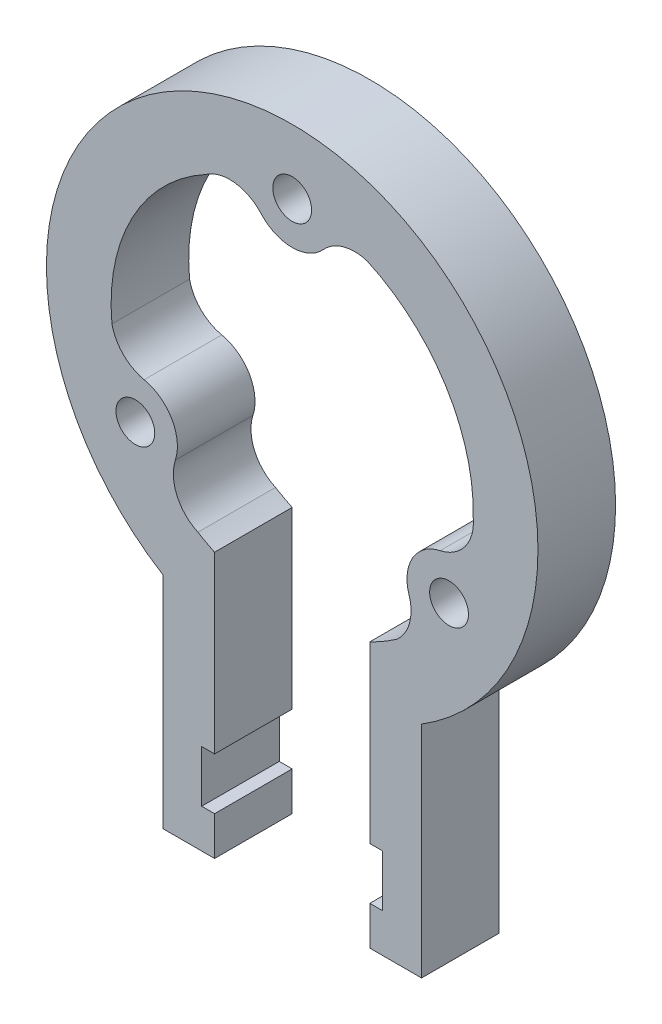
SolidWorks part; units mm, degrees
ref_plane "Plan de face" through (0, 0, 0) normal (0, 0, 1) x (1, 0, 0)
ref_plane "Plan de dessus" through (0, 0, 0) normal (0, 1, 0) x (1, 0, 0)
ref_plane "Plan de droite" through (0, 0, 0) normal (1, 0, 0) x (0, 0, -1)
sketch "Esquisse1" plane through (0, 0, 0) normal (0, 0, 1) x (1, 0, 0)
  line L0 (0, 14) -> (-12.125, -7.0011) construction
  line L1 (-12.125, -7.0011) -> (-10.6244, -7.0011) construction
  line L2 (12.125, -7.0011) -> (0, 14) construction
  line L3 (-6, -33.1555) -> (-6, -30.1555)
  line L5 (10, -16.1555) -> (10, -33.1555)
  line L6 (10, -33.1555) -> (6, -33.1555)
  line L7 (-10, -16.1555) -> (-10, -33.1555)
  line L8 (-7, -26.1555) -> (-6, -26.1555)
  line L9 (-7, -26.1555) -> (-7, -30.1555)
  line L10 (-7, -30.1555) -> (-6, -30.1555)
  line L11 (7, -26.1555) -> (7, -30.1555)
  line L12 (6, -33.1555) -> (6, -30.1555)
  line L13 (10, -7.0011) -> (12.125, -7.0011) construction
  line L14 (-6, -33.1555) -> (-10, -33.1555)
  line L15 (6, -30.1555) -> (7, -30.1555)
  line L16 (6, -26.1555) -> (7, -26.1555)
  line L17 (-6, -26.1555) -> (-6, -12.6491)
  line L18 (6, -26.1555) -> (6, -12.6491)
  arc A0 (10, -16.1555) -> (-10, -16.1555) centre (0, 0) ccw
  circle A2 centre (0, 14) radius 1.5
  arc A12 (-2.411, 11.8207) -> (2.411, 11.8207) centre (0, 14) ccw
  arc A16 (5.8094, 12.7378) -> (2.411, 11.8207) centre (4.8221, 9.6414) ccw
  arc A17 (-2.411, 11.8207) -> (-6.7074, 12.2887) centre (-4.8221, 9.6414) ccw
  arc A18 (-6.7074, 12.2887) -> (-13.9359, -1.3378) centre (0, 0) ccw
  arc A19 (8.1265, -11.4) -> (9.0315, -7.9984) centre (5.9386, -8.9967) ccw
  arc A20 (11.4425, -3.8223) -> (9.0315, -7.9984) centre (12.1244, -7) ccw
  arc A21 (11.4425, -3.8223) -> (13.996, -0.3356) centre (10.7607, -0.6447) ccw
  circle A22 centre (12.1244, -7) radius 1.5
  arc A23 (-13.9359, -1.3378) -> (-11.4425, -3.8223) centre (-10.7607, -0.6447) ccw
  arc A24 (-9.0315, -7.9984) -> (-11.4425, -3.8223) centre (-12.1244, -7) ccw
  arc A25 (-9.0315, -7.9984) -> (-7.2886, -11.9531) centre (-5.9386, -8.9967) ccw
  circle A26 centre (-12.1244, -7) radius 1.5
  arc A27 (-7.2886, -11.9531) -> (-6, -12.6491) centre (0, 0) ccw
  arc A28 (13.996, -0.3356) -> (5.8094, 12.7378) centre (0, 0) ccw
  circle A29 centre (0, 14) radius 3.25 construction
  arc A30 (6, -12.6491) -> (8.1265, -11.4) centre (0, 0) ccw
  point P31 (0, 0)
  point P35 (-10, -16.1555)
  point P36 (10, -16.1555)
  point P46 (6, -33.1555)
  point P49 (-6, -33.1555)
  dimension "D1" = 38
  dimension "D2" = 3
  dimension "D3" = 3
  dimension "D4" = 6.5
  dimension "D5" = 14
  dimension "D8" = 14
  dimension "D9" = 3.25
  dimension "D10" = 14
  dimension "D11" = 3.25
  dimension "D12" = 24.25
  dimension "D13" = 24.25
  dimension "D16" = 20
  dimension "D6" = 60
  dimension "D7" = 60
  dimension "D14" = 10.78
  dimension "D15" = 10.78
  dimension "D17" = 2.125
  dimension "D18" = 10
  dimension "D19" = 4
  dimension "D20" = 3
  dimension "D21" = 3
  dimension "D22" = 3
  dimension "D25" = 4
  dimension "D26" = 4
extrude "Boss.-Extru.2" add sketch "Esquisse1" along normal blind 6
